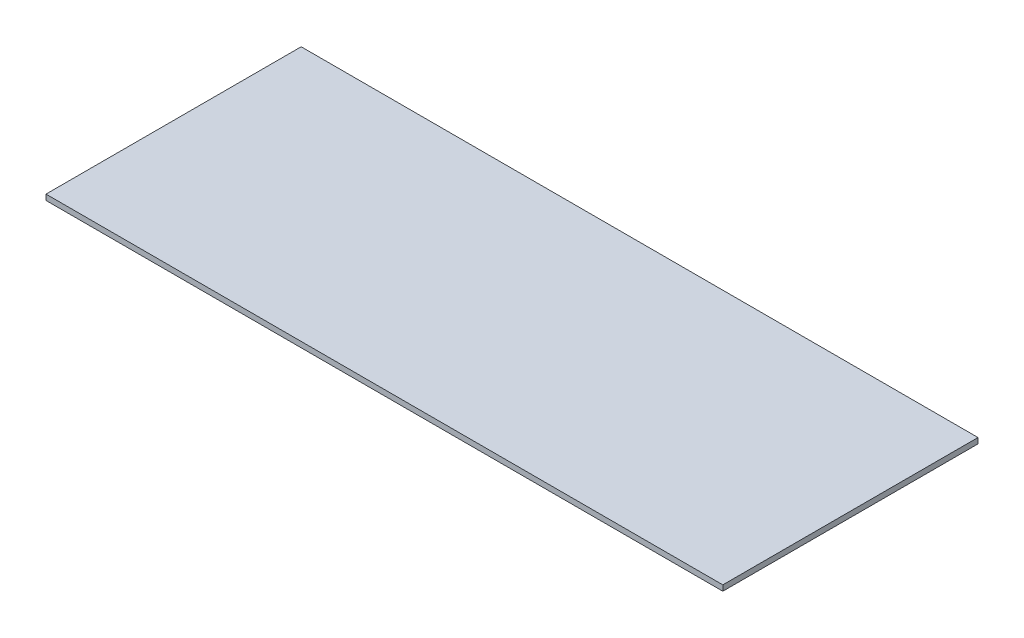
SolidWorks part; units mm, degrees
ref_plane "Front Plane" through (0, 0, 0) normal (0, 0, 1) x (1, 0, 0)
ref_plane "Top Plane" through (0, 0, 0) normal (0, 1, 0) x (1, 0, 0)
ref_plane "Right Plane" through (0, 0, 0) normal (1, 0, 0) x (0, 0, -1)
sketch "Sketch1" plane through (0, 0, 0) normal (0, 1, 0) x (1, 0, 0)
  line L1 (-1220, -460) -> (1220, -460)
  line L2 (-1220, -460) -> (-1220, 460)
  line L3 (-1220, 460) -> (1220, 460)
  line L4 (1220, -460) -> (1220, 460)
  line L5 (-1220, -460) -> (1220, 460) construction
  line L6 (-1220, 460) -> (1220, -460) construction
  point P0 (0, 0)
  dimension "D1" = 2440
  dimension "D2" = 920
extrude "Boss-Extrude1" add sketch "Sketch1" along normal blind 20
